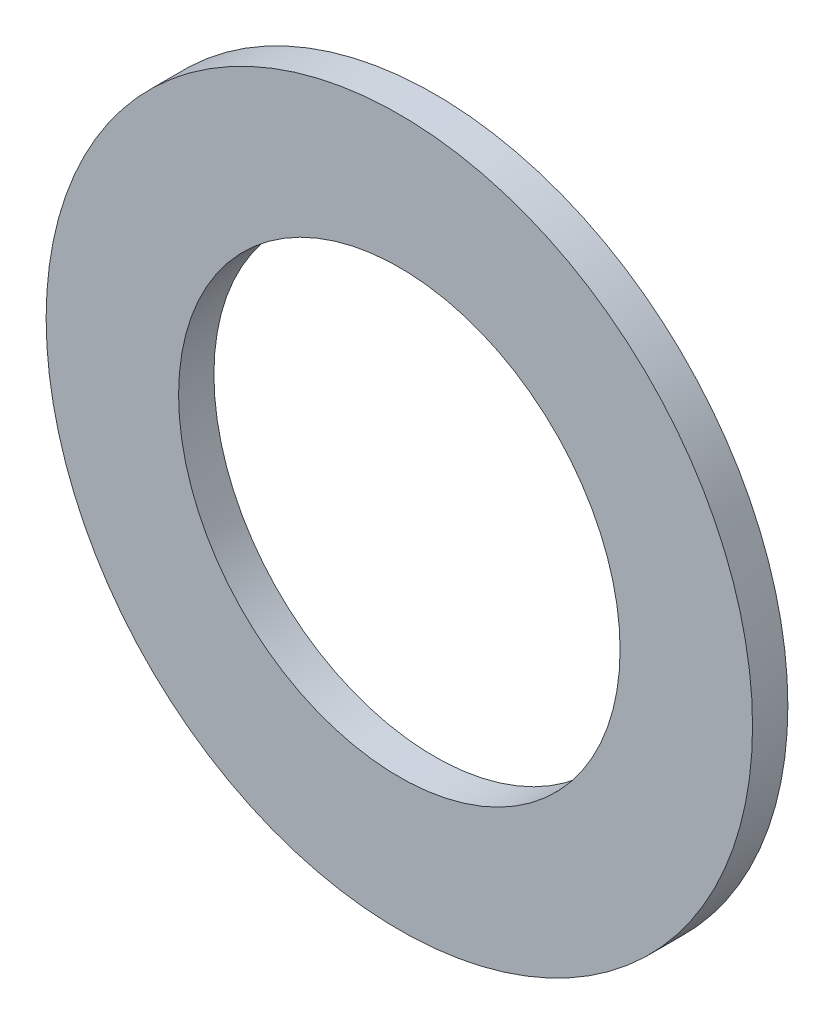
SolidWorks part; units mm, degrees
material "PVC Rigid"
ref_plane "Front Plane" through (0, 0, 0) normal (0, 0, 1) x (1, 0, 0)
ref_plane "Top Plane" through (0, 0, 0) normal (0, 1, 0) x (1, 0, 0)
ref_plane "Right Plane" through (0, 0, 0) normal (1, 0, 0) x (0, 0, -1)
sketch "Sketch1" plane through (0, 0, 0) normal (0, 0, 1) x (1, 0, 0)
  circle A0 centre (0, 0) radius 12.5
  circle A1 centre (0, 0) radius 20
  dimension "D1" = 25
  dimension "D2" = 40
extrude "Boss-Extrude1" add sketch "Sketch1" along normal blind 2
